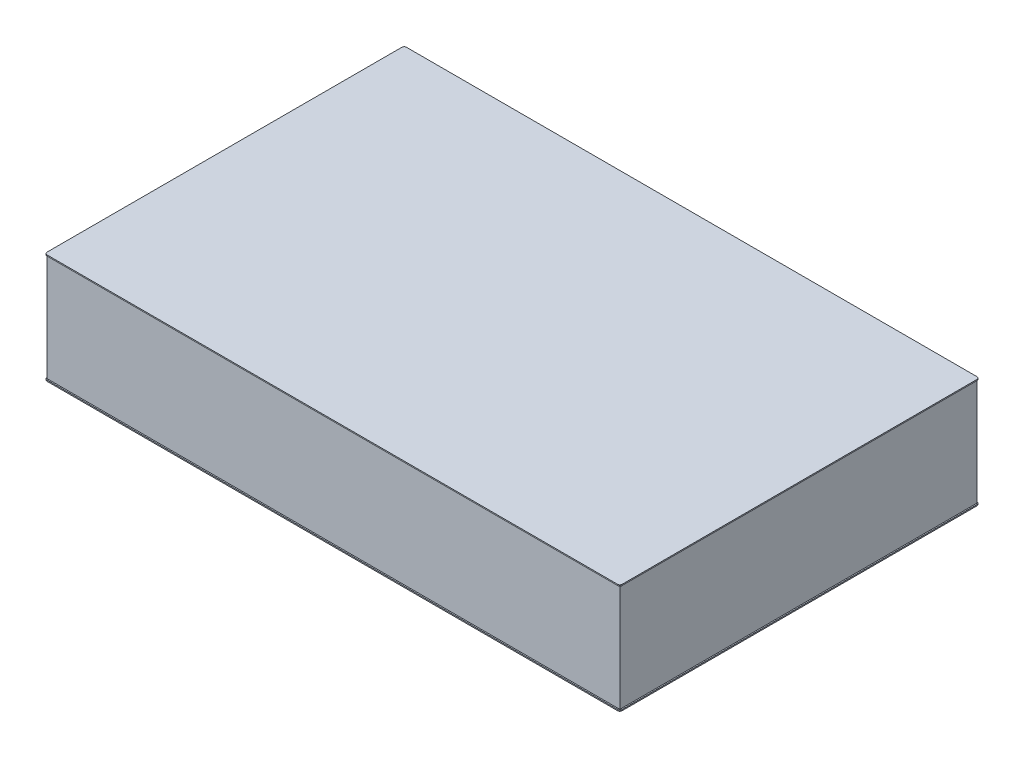
SolidWorks part; units mm, degrees
ref_plane "Front Plane" through (0, 0, 0) normal (0, 0, 1) x (1, 0, 0)
ref_plane "Top Plane" through (0, 0, 0) normal (0, 1, 0) x (1, 0, 0)
ref_plane "Right Plane" through (0, 0, 0) normal (1, 0, 0) x (0, 0, -1)
sketch "Sketch1" plane through (0, 0, 0) normal (0, 1, 0) x (1, 0, 0)
  line L0 (-1200, -740.348) -> (-1190.348, -740.348) construction
  line L1 (-1190.348, -750) -> (1190.348, -750)
  line L2 (-1200, -740.348) -> (-1200, 740.348)
  line L3 (-1190.348, 750) -> (1190.348, 750)
  line L4 (1200, -740.348) -> (1200, 740.348)
  line L5 (-1190.348, -740.348) -> (-1190.348, -750) construction
  line L6 (-1190.348, -740.348) -> (-1197.173, -747.173) construction
  line L7 (-1190.348, 750) -> (-1200, 750) construction
  line L8 (-1200, 750) -> (-1200, 740.348) construction
  line L9 (1200, -740.348) -> (1200, -750) construction
  line L10 (1200, -750) -> (1190.348, -750) construction
  line L11 (-1200, 750) -> (1200, -750) construction
  arc A0 (1190.348, -750) -> (1200, -740.348) centre (1190.348, -740.348) ccw
  arc A1 (1190.348, 750) -> (1200, 740.348) centre (1190.348, 740.348) cw
  arc A2 (-1200, 740.348) -> (-1190.348, 750) centre (-1190.348, 740.348) cw
  arc A3 (-1190.348, -750) -> (-1200, -740.348) centre (-1190.348, -740.348) cw
  point P13 (-1200, -750)
  dimension "D1" = 9.652
  dimension "D2" = 2400
  dimension "D3" = 1500
extrude "Boss-Extrude2" add sketch "Sketch1" against normal blind 4.8
sketch "Sketch4" plane through (0, -4.8, 0) normal (0, -1, 0) x (1, 0, 0)
  line L0 (-1200, 740.348) -> (-1190.348, 740.348) construction
  line L1 (-1195, 745) -> (1195, 745)
  line L2 (-1195, 745) -> (-1195, -745)
  line L3 (-1195, -745) -> (1195, -745)
  line L4 (1195, 745) -> (1195, -745)
  line L5 (-1190.348, 740.348) -> (-1190.348, 750) construction
  line L6 (-1190.348, 750) -> (-1190.348, 740.348) construction
  line L7 (-1193.8528, 743.8528) -> (-1190.348, 740.348) construction
  line L8 (-1195, 745) -> (1195, -745) construction
  point P11 (0, 0)
  dimension "D1" = 2390
  dimension "D2" = 1490
extrude "Boss-Extrude3" add sketch "Sketch4" along normal blind 447.4
sketch "Sketch5" plane through (0, -452.2, 0) normal (0, -1, 0) x (1, 0, 0)
  line L0 (-1190.348, -750) -> (-1190.348, -740.348) construction
  line L1 (-1190.348, -740.348) -> (-1200, -740.348) construction
  line L2 (1190.348, 750) -> (-1190.348, 750)
  line L3 (1200, 740.348) -> (1200, -740.348)
  line L4 (1190.348, -750) -> (-1190.348, -750)
  line L5 (-1200, 740.348) -> (-1200, -740.348)
  line L6 (-1190.348, -740.348) -> (-1197.173, -747.173) construction
  line L7 (1200, 740.348) -> (1200, 750) construction
  line L8 (1200, 750) -> (1190.348, 750) construction
  line L9 (-1200, -740.348) -> (-1200, -750) construction
  line L10 (-1190.348, -750) -> (-1200, -750) construction
  line L11 (-1200, -750) -> (1200, 750) construction
  arc A0 (-1200, 740.348) -> (-1190.348, 750) centre (-1190.348, 740.348) cw
  arc A1 (-1200, -740.348) -> (-1190.348, -750) centre (-1190.348, -740.348) ccw
  arc A2 (1190.348, -750) -> (1200, -740.348) centre (1190.348, -740.348) ccw
  arc A3 (1190.348, 750) -> (1200, 740.348) centre (1190.348, 740.348) cw
  dimension "D1" = 9.652
  dimension "D2" = 9.652
  dimension "D3" = 9.652
  dimension "D4" = 9.652
  dimension "D5" = 1500
  dimension "D6" = 2400
extrude "Boss-Extrude4" add sketch "Sketch5" along normal blind 4.8
hole_wizard "M6x1.0 Tapped Hole1" [suppressed] positions "Sketch7" profile "Sketch6" tap size "M6x1.0" standard "Ansi Metric"
sketch "Sketch7" plane through (0, 0, 0) normal (0, 1, 0) x (-1, 0, 0)
  line L0 (1200, -740.348) -> (1200, 740.348) construction
  line L1 (1190.348, 750) -> (-1190.348, 750) construction
  point P0 (1187.5, 737.5)
  dimension "D1" = 12.5
  dimension "D2" = 12.5
cosmetic thread "M6-1.0 Thread - Top Surface" [suppressed] parameters "D1"=4.8, "D2"=6
sketch "Sketch6" plane through (-1187.5, 0, 737.5) normal (1, 0, 0) x (0, 0, 1)
  line L0 (0, 0) -> (0, 6.3022)
  line L1 (0, 6.3022) -> (2.5, 4.8)
  line L2 (2.5, 4.8) -> (2.5, 0.2175)
  line L3 (2.5, 0.2175) -> (3.025, 0)
  line L5 (3.025, 0) -> (0, 0)
  line L6 (-2.5, 0.2175) -> (-3.025, 0) construction
  line L10 (0, 6.3022) -> (-2.5, 4.8) construction
  line L11 (0, -6.35) -> (0, 107.95) construction
  dimension "Tap Drill Dia." = 5
  dimension "Tap Drill Depth" = 4.8
  dimension "Near C'Sink Dia." = 6.05
  dimension "Near C'Sink Angle" = 135
  dimension "Drill Angle" = 118
pattern_linear "LPattern2" [suppressed] count 12 spacing 25 count 12 spacing 25
sketch "Sketch10" plane through (0, -457, 0) normal (0, -1, 0) x (1, 0, 0)
  line L0 (-641, 597.6) -> (-742.6, 597.6) construction
  line L1 (-641, 597.6) -> (-590.2, 685.5882) construction
  line L2 (-590.2, 685.5882) -> (-641, 597.6)
  line L3 (-641, 597.6) -> (-590.2, 509.6118) construction
  line L4 (-1190.348, 750) -> (1190.348, 750) construction
  line L5 (-1200, -740.348) -> (-1200, 740.348) construction
  circle A0 centre (-641, 597.6) radius 101.6 construction
  dimension "D1" = 152.4
  dimension "D3" = 203.2
  dimension "D2" = 559
  dimension "D4" = 120
  dimension "D5" = 120
hole_wizard "1/4-20 Tapped Hole5" [suppressed] positions "Sketch20" profile "Sketch19" tap size "1/4-20" standard "Ansi Inch"
sketch "Sketch20" plane through (0, -457, 0) normal (0, -1, 0) x (1, 0, 0)
  point P1 (-742.6, 597.6)
  point P4 (-590.2, 685.5882)
  point P7 (-590.2, 509.6118)
sketch "Sketch19" plane through (-742.6, -457, 597.6) normal (1, 0, 0) x (0, 0, -1)
  line L0 (0, 0) -> (0, 6.3338)
  line L1 (0, 6.3338) -> (2.5527, 4.8)
  line L2 (2.5527, 4.8) -> (2.5527, 0)
  line L5 (2.5527, 0) -> (0, 0)
  line L10 (0, 6.3338) -> (-2.5527, 4.8) construction
  line L11 (0, -6.35) -> (0, 107.95) construction
  dimension "Tap Drill Dia." = 5.1054
  dimension "Tap Drill Depth" = 4.8
  dimension "Drill Angle" = 118
cosmetic thread "Hole Thread1" [suppressed] parameters "D1"=0, "D2"=15.1054
cosmetic thread "Hole Thread2" [suppressed] parameters "D1"=0, "D2"=15.1054
cosmetic thread "Hole Thread3" [suppressed] parameters "D1"=0, "D2"=15.1054
mirror "Mirror1" [suppressed] about plane through (0, 0, 0) normal (1, 0, 0)
mirror "Mirror2" [suppressed] about plane through (0, 0, 0) normal (0, 0, 1)
